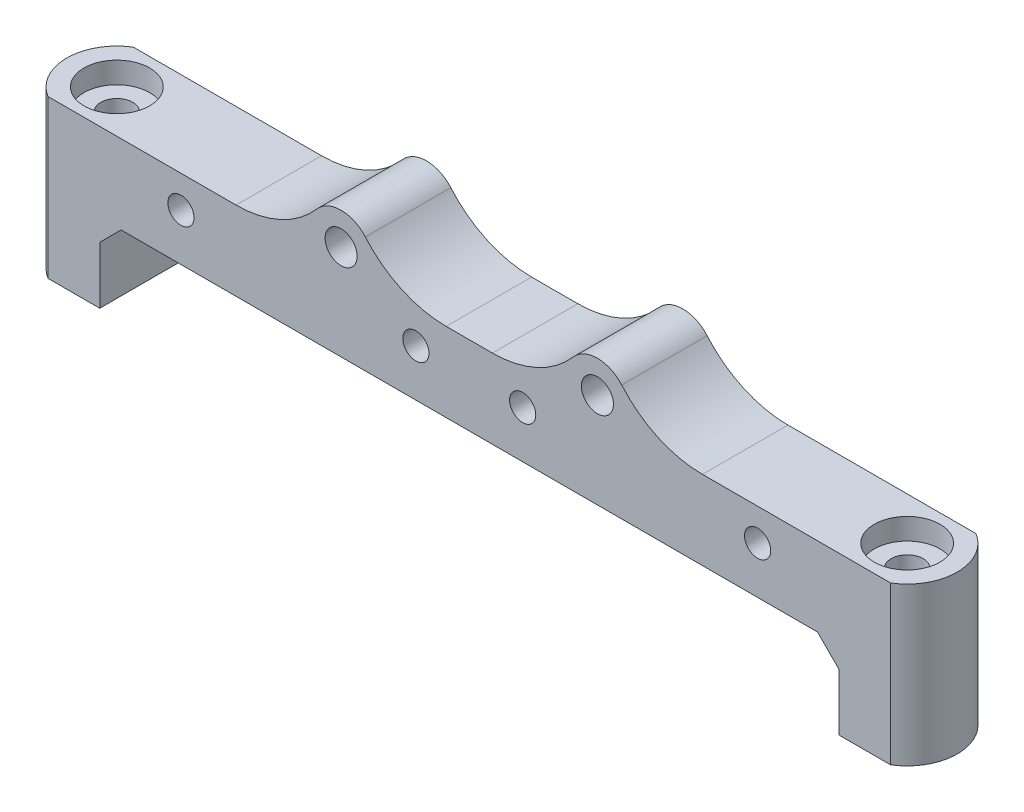
SolidWorks part; units mm, degrees
ref_plane "Front Plane" through (0, 0, 0) normal (0, 0, 1) x (1, 0, 0)
ref_plane "Top Plane" through (0, 0, 0) normal (0, 1, 0) x (1, 0, 0)
ref_plane "Right Plane" through (0, 0, 0) normal (1, 0, 0) x (0, 0, -1)
sketch "Sketch1" plane through (0, 0, 0) normal (0, 0, 1) x (1, 0, 0)
  line L0 (34.6, 7.35) -> (34.6, 0)
  line L5 (-34.5, 7.25) -> (34.5, 7.25) construction
  line L6 (-34.5, 7.25) -> (-34.5, 0) construction
  line L7 (-34.5, 0) -> (34.5, 0) construction
  line L8 (34.5, 7.25) -> (34.5, 0) construction
  line L9 (-34.6, 7.35) -> (34.6, 7.35)
  line L10 (-34.6, 7.35) -> (-34.6, 0)
  line L11 (-34.6, 0) -> (-39.45, 0)
  line L12 (-39.45, 0) -> (-39.45, 14.75)
  line L13 (-39.45, 14.75) -> (-14.5981, 14.75)
  line L14 (39.45, 14.75) -> (39.45, 0)
  line L15 (39.45, 0) -> (34.6, 0)
  line L16 (-39.45, 11.75) -> (39.45, 11.75) construction
  line L17 (14.5981, 14.75) -> (39.45, 14.75)
  line L18 (-9.4019, 14.75) -> (9.4019, 14.75)
  circle A0 centre (-5, 11.75) radius 1
  circle A1 centre (5, 11.75) radius 1
  circle A2 centre (27, 11.75) radius 1
  circle A3 centre (-27, 11.75) radius 1
  circle A4 centre (12, 16.25) radius 1.5
  circle A5 centre (-12, 16.25) radius 1.5
  arc A6 (14.5981, 14.75) -> (9.4019, 14.75) centre (12, 16.25) ccw
  arc A7 (-9.4019, 14.75) -> (-14.5981, 14.75) centre (-12, 16.25) ccw
  point P4 (0, 0)
  dimension "D7" = 5
  dimension "D9" = 2
  dimension "D10" = 22
  dimension "D11" = 22
  dimension "D12" = 24
  dimension "D15" = 6
  dimension "D8" = 5
  dimension "D16" = 3
  dimension "D1" = 69
  dimension "D2" = 7.25
  dimension "D4" = 4.85
  dimension "D5" = 14.75
  dimension "D6" = 3
  dimension "D13" = 12
  dimension "D14" = 4.5
  dimension "D3" = 0.1
extrude "Boss-Extrude1" add sketch "Sketch1" along normal blind 8
sketch "Sketch2" plane through (0, 0, 0) normal (0, -1, 0) x (1, 0, 0)
  line L6 (-39.45, 4) -> (39.45, 4) construction
  line L7 (-39.45, 8) -> (-39.45, 0) construction
  line L8 (39.45, 8) -> (39.45, 0) construction
  circle A0 centre (-37, 4) radius 1.5
  circle A1 centre (37, 4) radius 1.5
  dimension "D1" = 3
  dimension "D2" = 74
  dimension "D3" = 37
extrude "Cut-Extrude1" cut sketch "Sketch2" against normal through all
sketch "Sketch3" plane through (0, 14.75, 0) normal (0, 1, 0) x (1, 0, 0)
  line L0 (39.45, -8) -> (39.45, 0)
  line L1 (-39.45, -8) -> (-39.45, 0)
  line L2 (39.45, -8) -> (39.45, 0) construction
  arc A0 (39.45, -8) -> (39.45, 0) centre (37, -4) ccw
  arc A1 (-39.45, 0) -> (-39.45, -8) centre (-37, -4) ccw
extrude "Boss-Extrude2" add sketch "Sketch3" against normal up to vertex (14.75 mm away)
sketch "Sketch5" plane through (0, 14.75, 0) normal (0, 1, 0) x (1, 0, 0)
  circle A0 centre (37, -4) radius 3.075
  circle A1 centre (-37, -4) radius 3.075
  dimension "D1" = 6.15
extrude "Cut-Extrude2" cut sketch "Sketch5" against normal blind 2 and the other way through all contours A0 | A1
chamfer "Chamfer2" distance 2 angle 45 2 edges at (-34.6, 7.35, 4) (34.6, 7.35, 4)
fillet "Fillet1" radius 10 4 edges at (-14.5981, 14.75, 4) (-9.4019, 14.75, 4) (9.4019, 14.75, 4) (14.5981, 14.75, 4)
sketch "Sketch6" plane through (0, 0, 8) normal (0, 0, 1) x (1, 0, 0)
  circle A0 centre (-27, 11.75) radius 1.225
  circle A1 centre (-5, 11.75) radius 1.225
  circle A2 centre (5, 11.75) radius 1.225
  circle A3 centre (27, 11.75) radius 1.225
  dimension "D1" = 2.45
extrude "Cut-Extrude3" cut sketch "Sketch6" against normal blind 5
